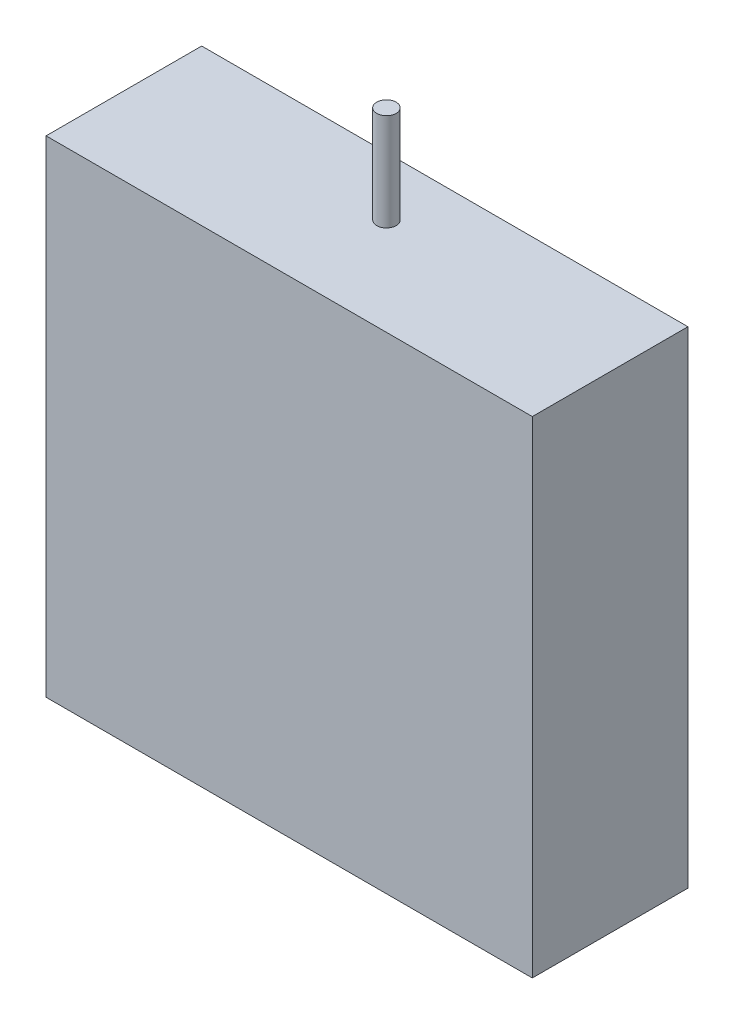
SolidWorks part; units mm, degrees
ref_plane "Płaszczyzna przednia" through (0, 0, 0) normal (0, 0, 1) x (1, 0, 0)
ref_plane "Płaszczyzna górna" through (0, 0, 0) normal (0, 1, 0) x (1, 0, 0)
ref_plane "Płaszczyzna prawa" through (0, 0, 0) normal (1, 0, 0) x (0, 0, -1)
sketch "Sketch1" plane through (0, 0, 0) normal (0, 0, 1) x (1, 0, 0)
  line L1 (-12.5, 12.5) -> (12.5, 12.5)
  line L2 (-12.5, 12.5) -> (-12.5, -12.5)
  line L3 (-12.5, -12.5) -> (12.5, -12.5)
  line L4 (12.5, 12.5) -> (12.5, -12.5)
  line L5 (-12.5, 12.5) -> (12.5, -12.5) construction
  line L6 (-12.5, -12.5) -> (12.5, 12.5) construction
  point P0 (0, 0)
  dimension "D1" = 25
  dimension "D2" = 25
extrude "Boss-Extrude1" add sketch "Sketch1" along normal blind 8
sketch "Sketch2" plane through (0, 12.5, 0) normal (0, 1, 0) x (1, 0, 0)
  line L0 (12.5, -8) -> (-12.5, -8) construction
  circle A0 centre (0, -3) radius 0.5
  dimension "D1" = 5
extrude "Boss-Extrude2" add sketch "Sketch2" along normal blind 5
